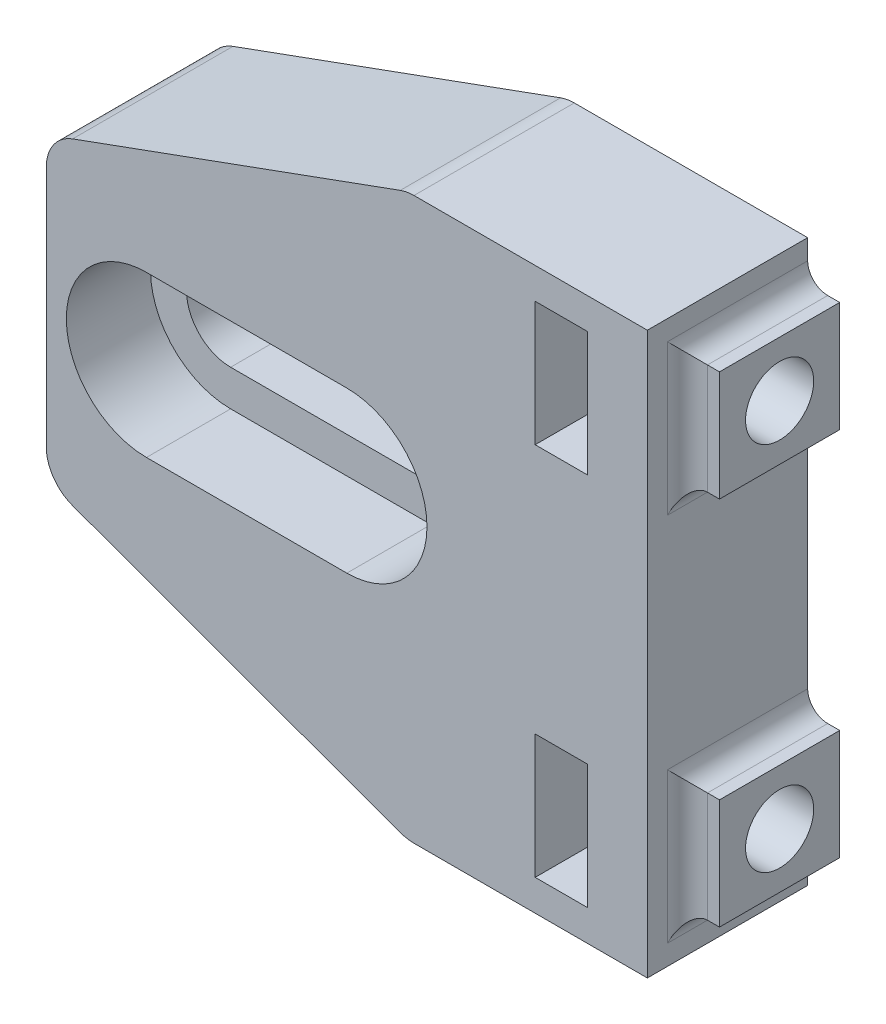
SolidWorks part; units mm, degrees
ref_plane "Plan de face" through (0, 0, 0) normal (0, 0, 1) x (1, 0, 0)
ref_plane "Plan de dessus" through (0, 0, 0) normal (0, 1, 0) x (1, 0, 0)
ref_plane "Plan de droite" through (0, 0, 0) normal (1, 0, 0) x (0, 0, -1)
sketch "Esquisse1" plane through (0, 0, 0) normal (0, 0, 1) x (1, 0, 0)
  line L1 (-8, 14) -> (22, 14)
  line L2 (-8, 14) -> (-8, -14)
  line L3 (-8, -14) -> (22, -14)
  line L4 (22, 14) -> (22, -14)
  dimension "D1" = 28
  dimension "D2" = 30
  dimension "D3" = 14
  dimension "D4" = 8
extrude "Boss.-Extru.1" add sketch "Esquisse1" along normal blind 8
sketch "Esquisse2" plane through (0, 0, 8) normal (0, 0, 1) x (1, 0, 0)
  line L0 (-8, 14) -> (-8, -14) construction
  line L1 (22, 14) -> (-8, 14) construction
  line L2 (-3, 0) -> (7, 0) construction
  line L3 (-3, 2.2) -> (7, 2.2)
  line L4 (-3, -2.2) -> (7, -2.2)
  arc A1 (-3, 2.2) -> (-3, -2.2) centre (-3, 0) ccw
  arc A2 (7, -2.2) -> (7, 2.2) centre (7, 0) ccw
  point P2 (2, 0)
  dimension "D1" = 14
  dimension "D4" = 2.2
  dimension "D2" = 5
  dimension "D3" = 14
  dimension "D5" = 10
extrude "Enlèv. mat.-Extru.1" cut sketch "Esquisse2" against normal through all
sketch "Esquisse3" plane through (0, 0, 8) normal (0, 0, 1) x (1, 0, 0)
  line L0 (-3, 0) -> (7, 0) construction
  line L1 (-3, 4) -> (7, 4)
  line L2 (-3, -4) -> (7, -4)
  arc A2 (-3, 4) -> (-3, -4) centre (-3, 0) ccw
  arc A3 (7, -4) -> (7, 4) centre (7, 0) ccw
  point P6 (2, 0)
  dimension "D2" = 4
extrude "Enlèv. mat.-Extru.2" cut sketch "Esquisse3" against normal blind 4.2
chamfer "Chanfrein1" distance 18 angle 20 2 edges at (-8, -14, 4) (-8, 14, 4)
fillet "Congé1" radius 2 4 edges at (10, -14, 4) (10, 14, 4) (-8, -7.4485, 4) (-8, 7.4485, 4)
sketch "Esquisse4" plane through (0, 0, 0) normal (0, 0, -1) x (-1, 0, 0)
  line L0 (-22, -14) -> (-22, 14) construction
  line L1 (-19, -12.45) -> (-16.4, -12.45)
  line L2 (-19, -12.45) -> (-19, -6.25)
  line L3 (-19, -6.25) -> (-16.4, -6.25)
  line L4 (-16.4, -12.45) -> (-16.4, -6.25)
  line L5 (-19, 6.25) -> (-16.4, 6.25)
  line L6 (-19, 6.25) -> (-19, 12.45)
  line L7 (-19, 12.45) -> (-16.4, 12.45)
  line L8 (-16.4, 6.25) -> (-16.4, 12.45)
  line L9 (-10.3527, -14) -> (-22, -14) construction
  dimension "D1" = 6.2
  dimension "D2" = 6.2
  dimension "D3" = 12.5
  dimension "D4" = 3
  dimension "D5" = 1.55
  dimension "D6" = 2.6
  dimension "D7" = 2.6
  dimension "D8" = 3
extrude "Enlèv. mat.-Extru.3" cut sketch "Esquisse4" against normal through all
sketch "Esquisse5" plane through (22, 0, 0) normal (1, 0, 0) x (0, 0, -1)
  line L0 (0, -14) -> (0, 14) construction
  line L1 (-8, -14) -> (0, -14) construction
  circle A0 centre (-3, 9.25) radius 1.7
  circle A1 centre (-3, -9.25) radius 1.7
  dimension "D1" = 3.4
  dimension "D2" = 3.4
  dimension "D3" = 18.5
  dimension "D4" = 3
  dimension "D5" = 4.75
  dimension "D6" = 3
extrude "Enlèv. mat.-Extru.4" cut sketch "Esquisse5" against normal blind 16
sketch "Esquisse6" plane through (22, 0, 0) normal (1, 0, 0) x (0, 0, -1)
  line L0 (0, -14) -> (0, 14) construction
  line L1 (0, -12) -> (-6, -12)
  line L2 (0, -12) -> (0, -6.5)
  line L3 (0, -6.5) -> (-6, -6.5)
  line L4 (-6, -12) -> (-6, -6.5)
  line L6 (0, 6.5) -> (-6, 6.5)
  line L7 (0, 6.5) -> (0, 12)
  line L8 (0, 12) -> (-6, 12)
  line L9 (-6, 6.5) -> (-6, 12)
  circle A0 centre (-3, -9.25) radius 1.7
  circle A1 centre (-3, 9.25) radius 1.7
  dimension "D1" = 5.5
  dimension "D2" = 6
  dimension "D3" = 2.75
  dimension "D4" = 5.5
  dimension "D5" = 2.75
  dimension "D6" = 6
extrude "Boss.-Extru.2" add sketch "Esquisse6" along normal blind 1.6
fillet "Congé2" radius 1 6 edges at (22, 6.5, 3) (22, -9.25, 6) (22, 9.25, 6) (22, 12, 3)
